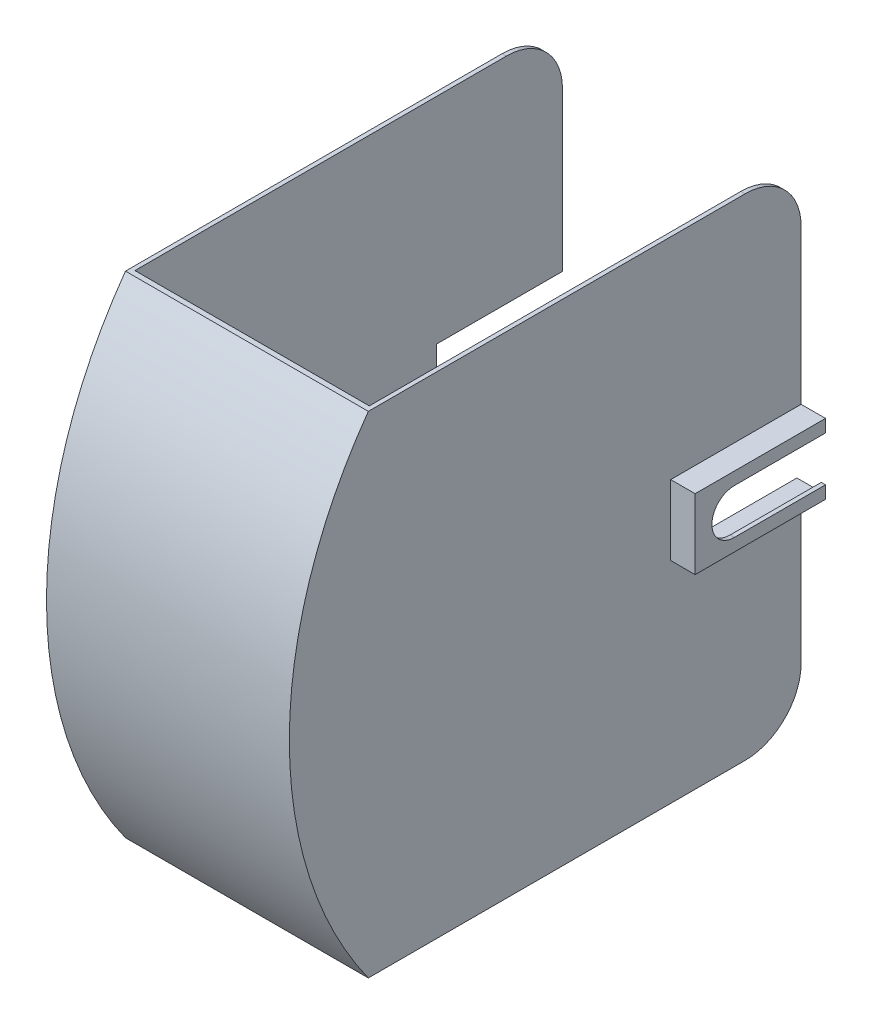
SolidWorks part; units mm, degrees
ref_plane "Front Plane" through (0, 0, 0) normal (0, 0, 1) x (1, 0, 0)
ref_plane "Top Plane" through (0, 0, 0) normal (0, 1, 0) x (1, 0, 0)
ref_plane "Right Plane" through (0, 0, 0) normal (1, 0, 0) x (0, 0, -1)
sketch "Sketch2" plane through (0, 0, 0) normal (0, 0, 1) x (1, 0, 0)
  line L1 (-54.9328, 53.0082) -> (-54.9328, 97.0082)
  line L2 (-54.9328, 97.0082) -> (-54.9328, 53.0082) construction
  line L3 (-72.3328, 53.0082) -> (-54.9328, 53.0082)
  line L5 (-54.9328, 97.0082) -> (-72.3328, 97.0082) construction
  line L6 (-72.3328, 97.0082) -> (-72.3328, 53.0082) construction
  line L7 (-72.3328, 97.0082) -> (-54.9328, 97.0082)
  line L9 (-72.3328, 53.0082) -> (-72.3328, 50.0082)
  line L10 (-72.3328, 50.0082) -> (-51.9328, 50.0082)
  line L11 (-51.9328, 50.0082) -> (-51.9328, 100.0082)
  line L12 (-51.9328, 100.0082) -> (-72.3328, 100.0082)
  line L13 (-72.3328, 100.0082) -> (-72.3328, 97.0082)
  dimension "D1" = 3
  dimension "D2" = 3
  dimension "D3" = 3
extrude "Boss-Extrude1" add sketch "Sketch2" against normal blind 90
sketch "Sketch3" plane through (-51.9328, 0, 0) normal (1, 0, 0) x (0, 0, -1)
  line L0 (25, 59.0082) -> (90, 59.0082)
  line L1 (25, 91.0082) -> (90, 91.0082)
  line L2 (90, 50.0082) -> (90, 100.0082) construction
  line L3 (90, 59.0082) -> (90, 91.0082)
  arc A0 (25, 91.0082) -> (25, 59.0082) centre (25, 75.0082) ccw
  dimension "D1" = 16
extrude "Cut-Extrude1" cut sketch "Sketch3" against normal blind 15
sketch "Sketch4" plane through (0, 50.0082, 0) normal (0, -1, 0) x (1, 0, 0)
  line L0 (-69.3328, -90) -> (-69.3328, 0)
  line L1 (-72.3328, -90) -> (-51.9328, -90) construction
  line L2 (-72.3328, 0) -> (-51.9328, 0) construction
  line L3 (-72.3328, -90) -> (-72.3328, 0) construction
  line L4 (-69.3328, 0) -> (-72.3328, 0)
  line L5 (-72.3328, 0) -> (-72.3328, -90)
  line L6 (-72.3328, -90) -> (-69.3328, -90)
  dimension "D1" = 3
extrude "Boss-Extrude3" add sketch "Sketch4" along normal blind 150
sketch "Sketch5" plane through (0, 100.0082, 0) normal (0, 1, 0) x (1, 0, 0)
  line L0 (-72.3328, 0) -> (-72.3328, 90)
  line L1 (-72.3328, 90) -> (-69.3328, 90)
  line L2 (-51.9328, 90) -> (-72.3328, 90) construction
  line L3 (-69.3328, 90) -> (-69.3328, 0)
  line L4 (-51.9328, 0) -> (-72.3328, 0) construction
  line L5 (-69.3328, 0) -> (-72.3328, 0)
  dimension "D1" = 3
extrude "Boss-Extrude4" add sketch "Sketch5" along normal blind 150
ref_plane "Plane1" through (-69.3328, -99.9918, 0) normal (0, 1, 0) x (1, 0, 0)
sketch "Sketch12" plane through (0, 0, 0) normal (0, 0, 1) x (1, 0, 0)
  line L1 (-51.9328, 100.0082) -> (-72.3328, 100.0082)
  line L2 (-51.9328, 100.0082) -> (-51.9328, 97.0082)
  line L3 (-51.9328, 97.0082) -> (-72.3328, 97.0082)
  line L4 (-72.3328, 100.0082) -> (-72.3328, 97.0082)
extrude "Boss-Extrude5" add sketch "Sketch12" along normal blind 3
sketch "Sketch13" plane through (0, 97.0082, 0) normal (0, -1, 0) x (1, 0, 0)
  line L1 (-51.9328, 0) -> (-72.3328, 0)
  line L2 (-51.9328, 0) -> (-51.9328, 3)
  line L3 (-51.9328, 3) -> (-72.3328, 3)
  line L4 (-72.3328, 0) -> (-72.3328, 3)
extrude "Boss-Extrude6" add sketch "Sketch13" along normal up to surface (47 mm away) up to face at (-60.6328, 50.0082, -45)
sketch "Sketch15" plane through (0, 0, 0) normal (0, 0, 1) x (1, 0, 0)
  line L2 (-72.3328, -99.9918) -> (-69.3328, -99.9918)
  line L3 (-72.3328, -99.9918) -> (-72.3328, 50.0082)
  line L4 (-72.3328, 50.0082) -> (-69.3328, 50.0082)
  line L5 (-69.3328, -99.9918) -> (-69.3328, 50.0082)
extrude "Boss-Extrude7" add sketch "Sketch15" along normal blind 3
sketch "Sketch16" plane through (0, 0, 0) normal (0, 0, 1) x (1, 0, 0)
  line L1 (-72.3328, 100.0082) -> (-69.3328, 100.0082)
  line L2 (-72.3328, 100.0082) -> (-72.3328, 250.0082)
  line L3 (-72.3328, 250.0082) -> (-69.3328, 250.0082)
  line L4 (-69.3328, 100.0082) -> (-69.3328, 250.0082)
extrude "Boss-Extrude8" add sketch "Sketch16" along normal blind 3
sketch "Sketch17" plane through (0, 0, 3) normal (0, 0, 1) x (1, 0, 0)
  line L1 (-72.3328, -99.9918) -> (-69.3328, -99.9918)
  line L2 (-72.3328, -99.9918) -> (-72.3328, 250.0082)
  line L3 (-72.3328, 250.0082) -> (-69.3328, 250.0082)
  line L4 (-69.3328, -99.9918) -> (-69.3328, 250.0082)
extrude "Boss-Extrude9" add sketch "Sketch17" along normal blind 293
sketch "Sketch18" plane through (-69.3328, 0, 0) normal (1, 0, 0) x (0, 0, -1)
  line L0 (-218.6699, -99.9918) -> (-296, -99.9918)
  line L1 (90, -99.9918) -> (-296, -99.9918) construction
  line L2 (-296, -99.9918) -> (-296, 250.0082)
  line L3 (-296, 250.0082) -> (-218.6699, 250.0082)
  line L4 (-296, 250.0082) -> (90, 250.0082) construction
  arc A0 (-218.6699, 250.0082) -> (-218.6699, -99.9918) centre (25, 75.0082) ccw
  dimension "D1" = 600
extrude "Cut-Extrude2" cut sketch "Sketch18" against normal blind 263
ref_plane "Center plane" through (-155.9328, 0, 0) normal (-1, 0, 0) x (0, 0, 1)
mirror "Mirror3" about plane through (-155.9328, 0, 0) normal (-1, 0, 0) of bodies 111
sketch "Sketch20" plane through (-72.3328, 0, 0) normal (-1, 0, 0) x (0, 0, 1)
  line L0 (-90, 250.0082) -> (218.6699, 250.0082) construction
  line L1 (214.9667, 250.0082) -> (218.6699, 250.0082)
  line L2 (218.6699, -99.9918) -> (-90, -99.9918) construction
  line L3 (214.9667, -99.9918) -> (218.6699, -99.9918)
  arc A0 (218.6699, -99.9918) -> (218.6699, 250.0082) centre (-25, 75.0082) ccw construction
  arc A1 (218.6699, -99.9918) -> (218.6699, 250.0082) centre (-25, 75.0082) ccw
  arc A2 (214.9667, -99.9918) -> (214.9667, 250.0082) centre (-25, 75.0082) ccw
  arc A3 (216.2332, -98.2418) -> (216.2332, 248.2582) centre (-25, 75.0082) ccw construction
  dimension "D1" = 3
extrude "Boss-Extrude10" add sketch "Sketch20" along normal up to surface (167.2 mm away)
fillet "Fillet1" radius 40 4 edges at (-241.0328, 250.0082, -90) (-241.0328, -99.9918, -90) (-70.8328, -99.9918, -90) (-70.8328, 250.0082, -90)
